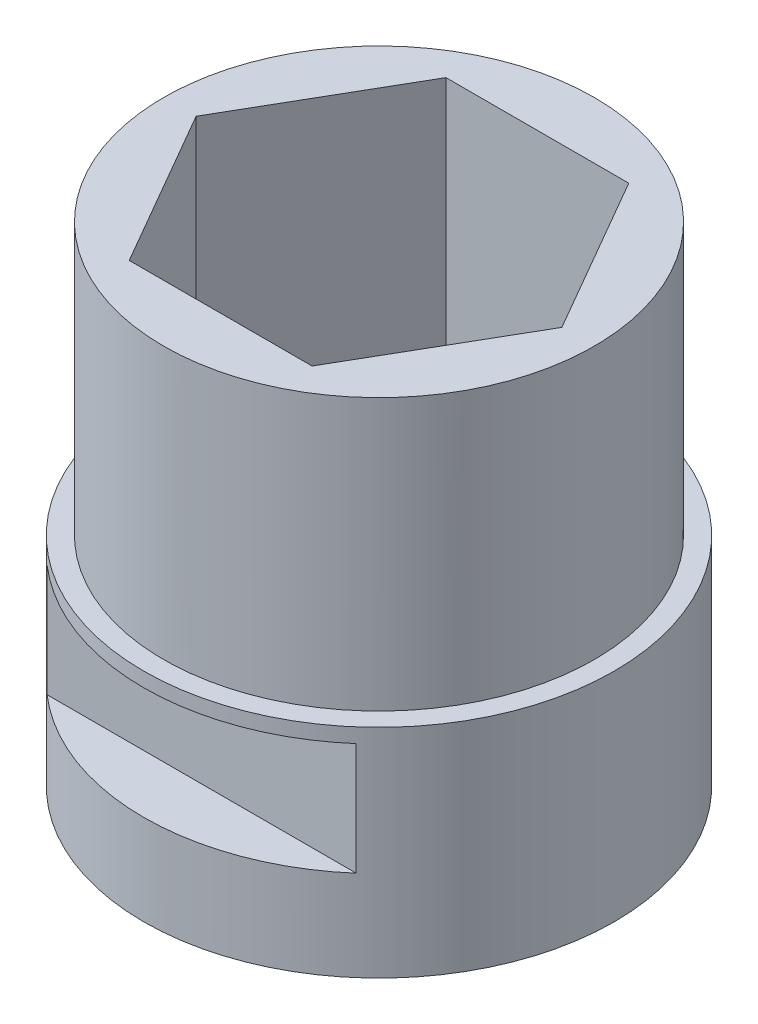
SolidWorks part; units mm, degrees
material "Polyester Resin"
ref_plane "Front Plane" through (0, 0, 0) normal (0, 0, 1) x (1, 0, 0)
ref_plane "Top Plane" through (0, 0, 0) normal (0, 1, 0) x (1, 0, 0)
ref_plane "Right Plane" through (0, 0, 0) normal (1, 0, 0) x (0, 0, -1)
sketch "Sketch1" plane through (0, 0, 0) normal (0, 1, 0) x (1, 0, 0)
  line L1 (-3.2079, 5.5562) -> (-6.4158, 0)
  line L2 (-6.4158, 0) -> (-3.2079, -5.5562)
  line L3 (-3.2079, -5.5562) -> (3.2079, -5.5562)
  line L4 (3.2079, -5.5562) -> (6.4158, 0)
  line L5 (6.4158, 0) -> (3.2079, 5.5562)
  line L6 (3.2079, 5.5562) -> (-3.2079, 5.5562)
  circle A0 centre (0, 0) radius 5.5562 construction
  circle A1 centre (0, 0) radius 7.5565
  dimension "D2" = 15.113
  dimension "D1" = 11.1125
extrude "Boss-Extrude1" add sketch "Sketch1" along normal blind 16.51
sketch "Sketch2" plane through (0, 0, 0) normal (0, -1, 0) x (1, 0, 0)
  circle A0 centre (0, 0) radius 7.5565
  circle A1 centre (0, 0) radius 3.3
  dimension "D1" = 6.6
extrude "Boss-Extrude2" add sketch "Sketch2" along normal blind 0.635
sketch "Sketch4" plane through (0, -0.635, 0) normal (0, -1, 0) x (1, 0, 0)
  circle A0 centre (0, 0) radius 7.5565
  circle A1 centre (0, 0) radius 8.255
  dimension "D1" = 16.51
extrude "Boss-Extrude3" add sketch "Sketch4" against normal blind 7.62
sketch "Sketch3" plane through (0, 0, 0) normal (1, 0, 0) x (0, 0, -1)
  line L0 (-6.223, 6.477) -> (-6.223, 2.54)
  line L1 (6.223, 6.477) -> (6.223, 2.54)
  line L2 (-7.5565, -0.635) -> (7.5565, -0.635) construction
  line L3 (-6.223, 6.477) -> (-8.7958, 6.477)
  line L4 (-8.7958, 6.477) -> (-8.7958, 2.54)
  line L5 (-8.7958, 2.54) -> (-6.223, 2.54)
  line L6 (6.223, 6.477) -> (8.4791, 6.477)
  line L7 (8.4791, 6.477) -> (8.4791, 2.54)
  line L8 (8.4791, 2.54) -> (6.223, 2.54)
  dimension "D1" = 12.446
  dimension "D2" = 6.223
  dimension "D3" = 3.937
  dimension "D4" = 3.937
  dimension "D5" = 3.175
  dimension "D6" = 3.175
extrude "Cut-Extrude1" cut sketch "Sketch3" against normal through all and the other way through all
equation "\"AB_Central_Bushing_Length\"= .4724in"
equation "\"Solid_Length\"= .025in"
equation "\"Hex_Length\"=0.65"
equation "\"D1@Boss-Extrude1\"= \"Hex_Length\""
equation "\"D1@Boss-Extrude2\"=\"Solid_Length\""
equation "\"Cutout_Angle\"= 80"
